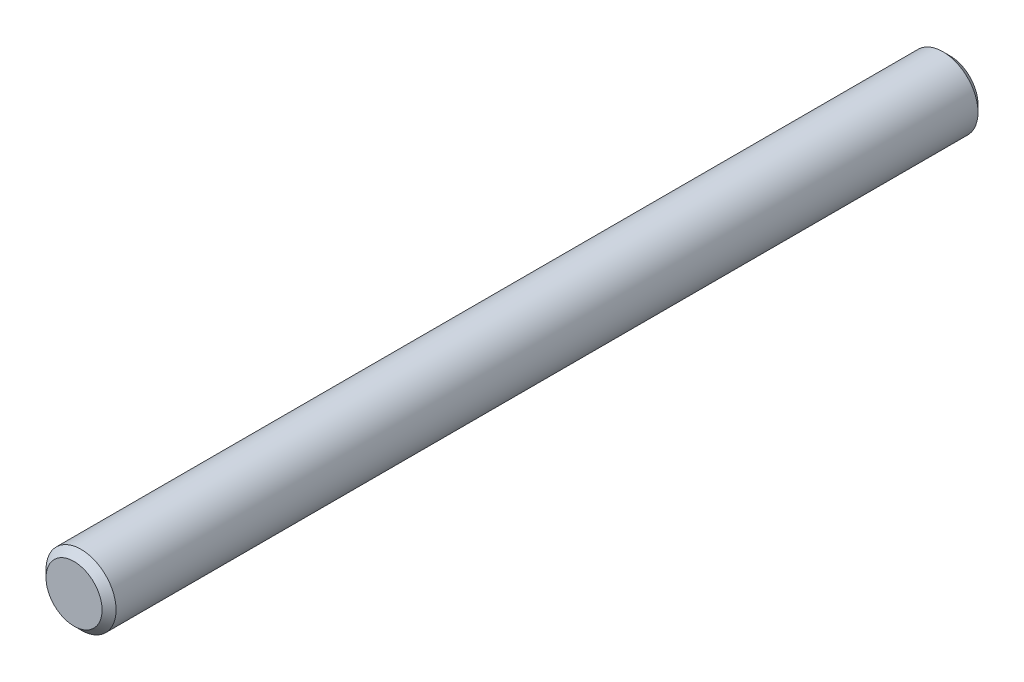
SolidWorks part; units mm, degrees
ref_plane "Front" through (0, 0, 0) normal (0, 0, 1) x (1, 0, 0)
ref_plane "Top" through (0, 0, 0) normal (0, 1, 0) x (1, 0, 0)
ref_plane "Right" through (0, 0, 0) normal (1, 0, 0) x (0, 0, -1)
sketch "Sketch1" plane through (0, 0, 0) normal (0, 0, 1) x (1, 0, 0)
  circle A0 centre (0, 0) radius 4
  dimension "D1" = 8
extrude "Extrude1" add sketch "Sketch1" along normal mid plane 200
chamfer "Chamfer1" distance 0.8 angle 45 2 edges at (4, 0, -100) (4, 0, 100)
sketch "Sketch2" plane through (0, 0, 0) normal (1, 0, 0) x (0, 0, -1)
  line L0 (99.2, 4) -> (-99.2, 4) construction
  line L1 (0, 4) -> (103.9825, 4)
  line L2 (0, 4) -> (0, -4.7197)
  line L3 (0, -4.7197) -> (103.9825, -4.7197)
  line L4 (103.9825, 4) -> (103.9825, -4.7197)
extrude "Cut-Extrude1" cut sketch "Sketch2" against normal through all both and the other way through all
chamfer "Chamfer2" distance 0.8 angle 45 1 edges at (4, 0, 0)
equation "\"D1@Chamfer1\" = \"D1@Sketch1\" * .1"
